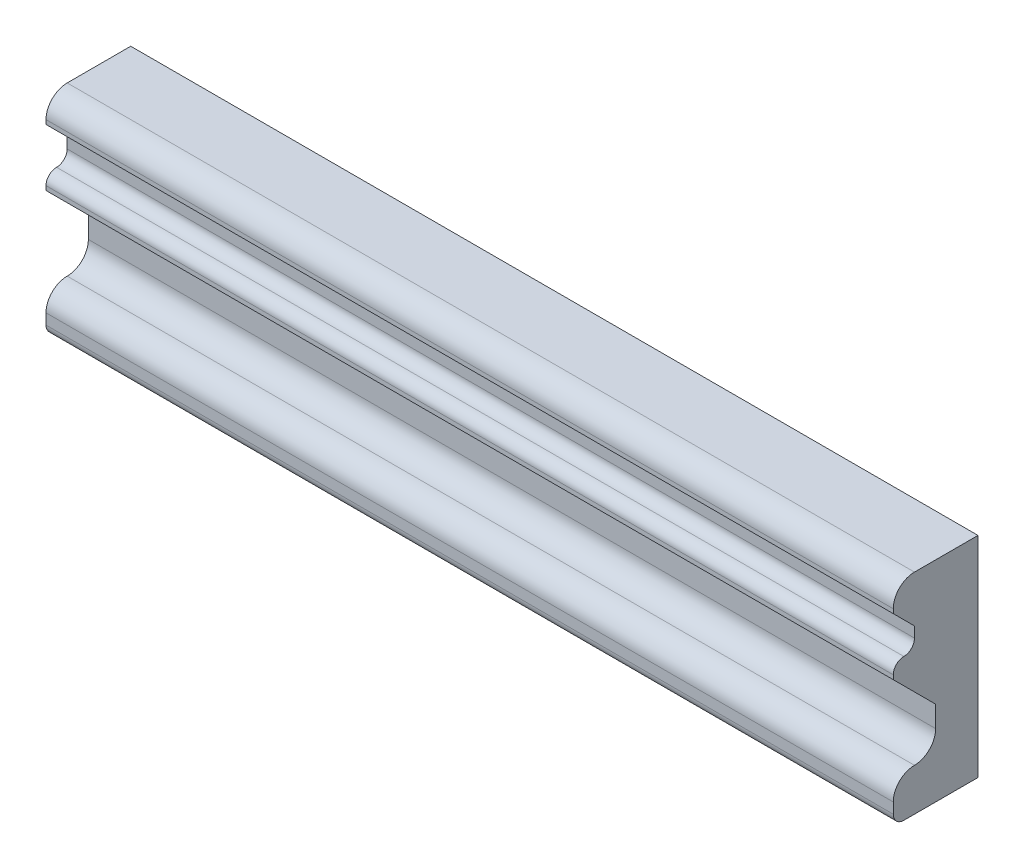
SolidWorks part; units mm, degrees
ref_plane "Front" through (0, 0, 0) normal (0, 0, 1) x (1, 0, 0)
ref_plane "Top" through (0, 0, 0) normal (0, 1, 0) x (1, 0, 0)
ref_plane "Right" through (0, 0, 0) normal (1, 0, 0) x (0, 0, -1)
sketch "Croquis1" plane through (0, 0, 0) normal (1, 0, 0) x (0, 0, -1)
  line L0 (-20, 37.5) -> (-20, 39.5)
  line L1 (20, -49.5) -> (-15, -49.5)
  line L2 (20, -49.5) -> (20, 49.5)
  line L3 (20, 49.5) -> (-10, 49.5)
  line L4 (-20, -44.5) -> (-20, -39.5)
  line L5 (20, -49.5) -> (-20, 49.5) construction
  line L6 (20, 49.5) -> (0, 0) construction
  line L10 (-10, 27.5) -> (-10, 22.5)
  line L14 (0, -19.5) -> (0, -9.5)
  line L15 (-20, 10.5) -> (-20, 12.5)
  line L16 (-20, 10.5) -> (0, -9.5)
  line L17 (-2.7338, -6.7662) -> (-20, -49.5) construction
  line L18 (-20, 37.5) -> (-10, 27.5)
  arc A0 (-10, -29.5) -> (0, -19.5) centre (-10, -19.5) ccw
  arc A2 (-10, 49.5) -> (-20, 39.5) centre (-10, 39.5) ccw
  arc A3 (-10, -29.5) -> (-20, -39.5) centre (-10, -39.5) ccw
  arc A5 (-15, 17.5) -> (-10, 22.5) centre (-15, 22.5) ccw
  arc A6 (-15, 17.5) -> (-20, 12.5) centre (-15, 12.5) ccw
  arc A7 (-15, -49.5) -> (-20, -44.5) centre (-15, -44.5) cw
  point P0 (0, 0)
  dimension "D1" = 10
  dimension "D2" = 10
  dimension "D8" = 5
  dimension "D9" = 5
  dimension "D12" = 5
  dimension "D3" = 40
  dimension "D4" = 20
  dimension "D5" = 45
  dimension "D6" = 10
  dimension "D7" = 2
  dimension "D10" = 10
  dimension "D11" = 10
  dimension "D13" = 45
  dimension "D14" = 20
  dimension "D15" = 2
extrude "Saliente-Extruir1" add sketch "Croquis1" along normal blind 400
